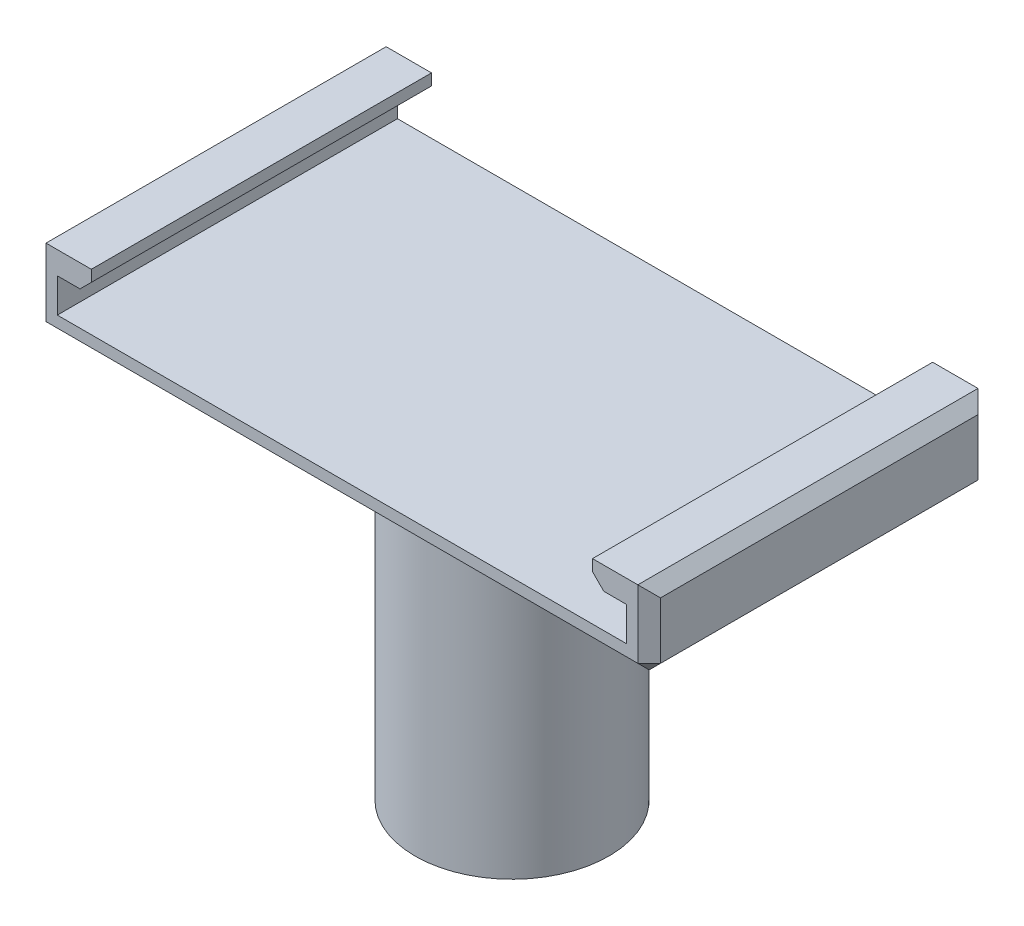
SolidWorks part; units mm, degrees
ref_plane "Front Plane" through (0, 0, 0) normal (0, 0, 1) x (1, 0, 0)
ref_plane "Top Plane" through (0, 0, 0) normal (0, 1, 0) x (1, 0, 0)
ref_plane "Right Plane" through (0, 0, 0) normal (1, 0, 0) x (0, 0, -1)
sketch "Sketch1" plane through (0, 0, 0) normal (0, 1, 0) x (1, 0, 0)
  circle A0 centre (0, 0) radius 7.55
  circle A1 centre (0, 0) radius 8.55
  dimension "D1" = 15.1
  dimension "D2" = 1
extrude "Boss-Extrude1" add sketch "Sketch1" along normal blind 30
sketch "Sketch2" plane through (0, 30, 0) normal (0, 1, 0) x (1, 0, 0)
  circle A0 centre (0, 0) radius 8.55
extrude "Boss-Extrude2" add sketch "Sketch2" against normal blind 2
sketch "Sketch3" plane through (0, 30, 0) normal (0, 1, 0) x (1, 0, 0)
  line L0 (27.1, -15) -> (27.1, 15)
  line L1 (-25, -15) -> (25, -15)
  line L3 (-25, 15) -> (25, 15)
  line L8 (-27.1, -15) -> (-27.1, 15)
  line L10 (25, 15) -> (27.1, 15)
  line L11 (25, -15) -> (27.1, -15)
  line L12 (-25, -15) -> (-27.1, -15)
  line L13 (-25, 15) -> (-27.1, 15)
  line L15 (-27.1, 17.1) -> (27.1, 17.1) construction
  line L16 (-27.1, -17.1) -> (-27.1, 17.1) construction
  line L17 (-27.1, -17.1) -> (27.1, -17.1) construction
  line L18 (25, -15) -> (25, 15) construction
  line L19 (-25, -15) -> (-25, 15) construction
  line L20 (27.1, -17.1) -> (27.1, 17.1) construction
  point P0 (0, 0)
  dimension "D1" = 30
  dimension "D2" = 50
  dimension "D3" = 2.1
extrude "Boss-Extrude3" add sketch "Sketch3" along normal blind 2
sketch "Sketch4" plane through (0, 32, 0) normal (0, 1, 0) x (1, 0, 0)
  line L0 (-27.1, -15) -> (27.1, -15) construction
  line L1 (-27.1, 15) -> (-25.1, 15)
  line L2 (-27.1, 15) -> (-27.1, -15)
  line L3 (-27.1, -15) -> (-25.1, -15)
  line L4 (-25.1, 15) -> (-25.1, -15)
  line L6 (27.1, 15) -> (25.1, 15)
  line L7 (27.1, 15) -> (27.1, -15)
  line L8 (27.1, -15) -> (25.1, -15)
  line L9 (25.1, 15) -> (25.1, -15)
  dimension "D1" = 2
  dimension "D2" = 2
extrude "Boss-Extrude4" add sketch "Sketch4" along normal blind 5
sketch "Sketch6" plane through (-25.1, 0, 0) normal (1, 0, 0) x (0, 0, -1)
  line L0 (15, 37) -> (15, 30) construction
  line L1 (-15, 37) -> (15, 37)
  line L2 (-15, 37) -> (-15, 35)
  line L3 (-15, 35) -> (15, 35)
  line L4 (15, 37) -> (15, 35)
  dimension "D1" = 2
extrude "Boss-Extrude5" add sketch "Sketch6" along normal blind 3
sketch "Sketch7" plane through (25.1, 0, 0) normal (-1, 0, 0) x (0, 0, 1)
  line L1 (-15, 37) -> (15, 37)
  line L2 (-15, 37) -> (-15, 35)
  line L3 (-15, 35) -> (15, 35)
  line L4 (15, 37) -> (15, 35)
extrude "Boss-Extrude6" add sketch "Sketch7" along normal blind 3
chamfer "Chamfer1" distance 3 angle 45 1 edges at (0, 30, 8.55)
chamfer "Chamfer2" distance 1 angle 45 2 edges at (-22.1, 35, 0) (22.1, 35, 0)
chamfer "Chamfer3" distance 1 angle 45 10 edges at (-27.1, 33.5, -15) (27.1, 33.5, -15) (27.1, 37, 0) (27.1, 33.5, 15) (-27.1, 37, 0) (-27.1, 33.5, 15) (0, 30, 15) (-27.1, 30, 0) (0, 30, -15) (27.1, 30, 0)
